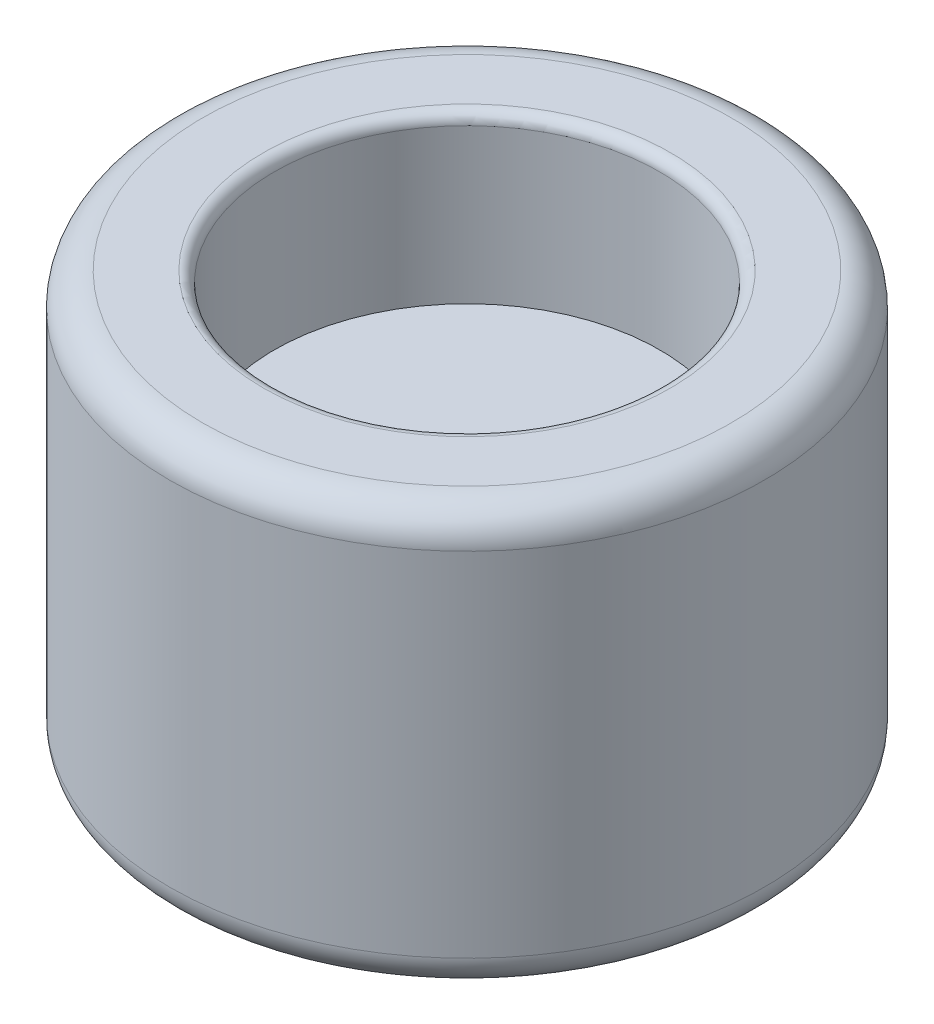
SolidWorks part; units mm, degrees
material "Mousse de polyuréthane rigide"
ref_plane "Plan de face" through (0, 0, 0) normal (0, 0, 1) x (1, 0, 0)
ref_plane "Plan de dessus" through (0, 0, 0) normal (0, 1, 0) x (1, 0, 0)
ref_plane "Plan de droite" through (0, 0, 0) normal (1, 0, 0) x (0, 0, -1)
sketch "Esquisse1" plane through (0, 0, 0) normal (0, 1, 0) x (1, 0, 0)
  circle A0 centre (0, 0) radius 27
  dimension "D1" = 54
extrude "Boss.-Extru.1" add sketch "Esquisse1" along normal blind 38
fillet "Congé1" radius 3 1 edges at (0, 38, 27)
fillet "Congé2" radius 3 1 edges at (0, 0, 27)
sketch "Esquisse2" plane through (0, 0, 0) normal (0, -1, 0) x (1, 0, 0)
  circle A0 centre (0, 0) radius 17.5
  dimension "D1" = 35
extrude "Enlèv. mat.-Extru.1" cut sketch "Esquisse2" against normal blind 15
sketch "Esquisse3" plane through (0, 38, 0) normal (0, 1, 0) x (1, 0, 0)
  circle A0 centre (0, 0) radius 17.5
  dimension "D1" = 35
extrude "Enlèv. mat.-Extru.2" cut sketch "Esquisse3" against normal blind 15
sketch "Esquisse4" plane through (0, 23, 0) normal (0, 1, 0) x (1, 0, 0)
  circle A0 centre (0, 0) radius 3
  dimension "D1" = 6
extrude "Enlèv. mat.-Extru.3" cut sketch "Esquisse4" against normal blind 15
fillet "Congé3" radius 1 1 edges at (0, 38, 17.5)
fillet "Congé4" radius 1 1 edges at (0, 0, -17.5)
